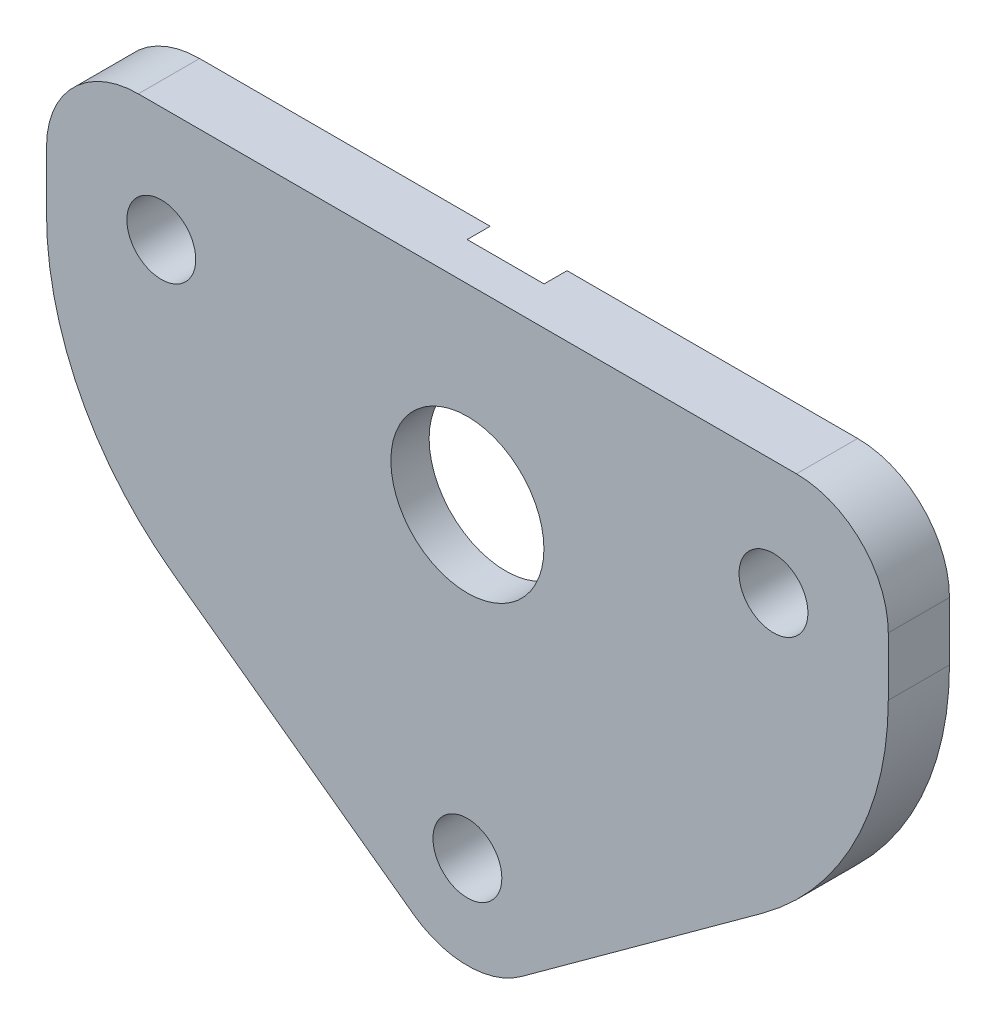
SolidWorks part; units mm, degrees
ref_plane "Plan de face" through (0, 0, 0) normal (0, 0, 1) x (1, 0, 0)
ref_plane "Plan de dessus" through (0, 0, 0) normal (0, 1, 0) x (1, 0, 0)
ref_plane "Plan de droite" through (0, 0, 0) normal (1, 0, 0) x (0, 0, -1)
sketch "Esquisse1" plane through (0, 0, 0) normal (0, 0, 1) x (1, 0, 0)
  line L0 (-55, 20) -> (-27.5, 0)
  line L1 (-55, 40) -> (0, 40)
  line L2 (-55, 40) -> (-55, 20)
  line L4 (0, 40) -> (0, 20)
  line L5 (-27.5, 0) -> (0, 20)
  circle A0 centre (-27.5, 27.5) radius 5
  circle A1 centre (-47.5, 32.5) radius 2.25
  circle A2 centre (-7.5, 32.5) radius 2.25
  circle A3 centre (-27.5, 7.5) radius 2.25
  dimension "D3" = 4.5
  dimension "D4" = 4.5
  dimension "D5" = 4.5
  dimension "D6" = 10
  dimension "D7" = 20
  dimension "D8" = 20
  dimension "D9" = 5
  dimension "D10" = 5
  dimension "D11" = 20
  dimension "D12" = 7.5
  dimension "D13" = 7.5
  dimension "D14" = 7.5
  dimension "D15" = 7.5
  dimension "D1" = 55
  dimension "D2" = 40
extrude "Boss.-Extru.1" add sketch "Esquisse1" along normal blind 4
fillet "Congé2" radius 6 3 edges at (-27.5, 0, 2) (-55, 40, 2) (0, 40, 2)
fillet "Congé3" radius 20 2 edges at (-55, 20, 2) (0, 20, 2)
sketch "Esquisse4" plane through (0, 0, 0) normal (0, 0, -1) x (-1, 0, 0)
  circle A0 centre (27.5, 27.5) radius 12.75
  dimension "D1" = 25.5
extrude "Enlèv. mat.-Extru.20" cut sketch "Esquisse4" against normal blind 1.5
